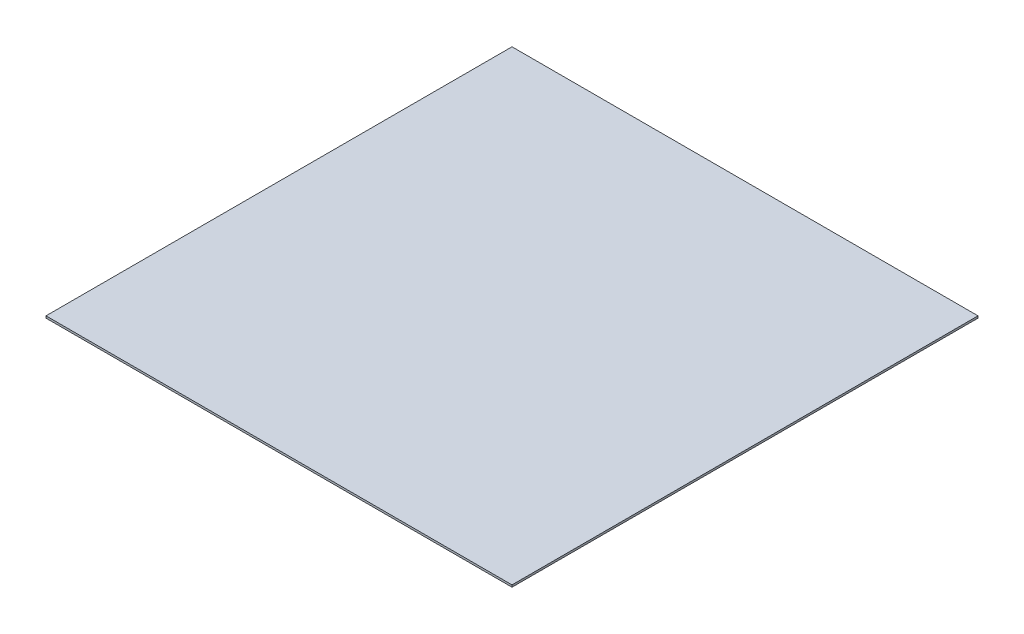
SolidWorks part; units mm, degrees
ref_plane "Front Plane" through (0, 0, 0) normal (0, 0, 1) x (1, 0, 0)
ref_plane "Top Plane" through (0, 0, 0) normal (0, 1, 0) x (1, 0, 0)
ref_plane "Right Plane" through (0, 0, 0) normal (1, 0, 0) x (0, 0, -1)
sketch "Sketch1" plane through (0, 0, 0) normal (0, 1, 0) x (1, 0, 0)
  line L1 (-149, 149) -> (149, 149)
  line L2 (-149, 149) -> (-149, -149)
  line L3 (-149, -149) -> (149, -149)
  line L4 (149, 149) -> (149, -149)
  line L5 (-149, 149) -> (149, -149) construction
  line L6 (-149, -149) -> (149, 149) construction
  point P0 (0, 0)
  dimension "D1" = 298
  dimension "D2" = 298
extrude "Boss-Extrude1" add sketch "Sketch1" along normal blind 1.3
